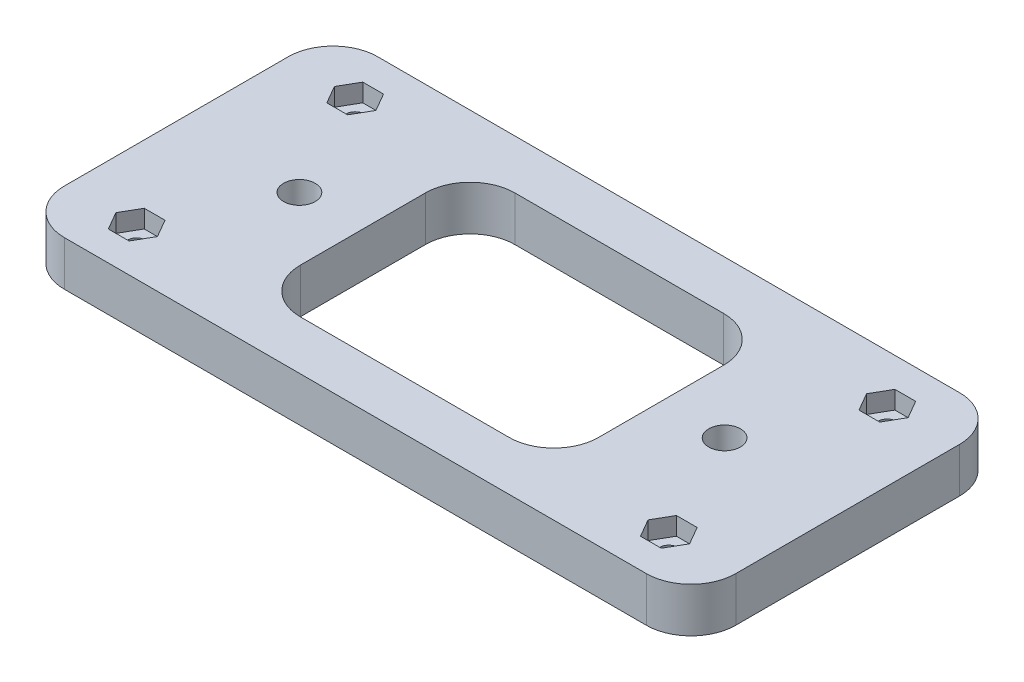
SolidWorks part; units mm, degrees
ref_plane "Front Plane" through (0, 0, 0) normal (0, 0, 1) x (1, 0, 0)
ref_plane "Top Plane" through (0, 0, 0) normal (0, 1, 0) x (1, 0, 0)
ref_plane "Right Plane" through (0, 0, 0) normal (1, 0, 0) x (0, 0, -1)
sketch "Sketch1" plane through (0, 0, 0) normal (0, 1, 0) x (1, 0, 0)
  line L0 (-47.625, 0) -> (47.625, 0) construction
  line L1 (41.275, 22.225) -> (-41.275, 22.225)
  line L2 (47.625, 15.875) -> (47.625, -15.875)
  line L3 (41.275, -22.225) -> (-41.275, -22.225)
  line L4 (-47.625, 15.875) -> (-47.625, -15.875)
  line L5 (47.625, 22.225) -> (-47.625, -22.225) construction
  line L6 (47.625, -22.225) -> (-47.625, 22.225) construction
  line L7 (0, 22.225) -> (0, -22.225) construction
  arc A0 (41.275, 22.225) -> (47.625, 15.875) centre (41.275, 15.875) cw
  arc A1 (47.625, -15.875) -> (41.275, -22.225) centre (41.275, -15.875) cw
  arc A2 (-41.275, -22.225) -> (-47.625, -15.875) centre (-41.275, -15.875) cw
  arc A3 (-41.275, 22.225) -> (-47.625, 15.875) centre (-41.275, 15.875) ccw
  circle A6 centre (-37.75, 15.5) radius 1.3
  circle A7 centre (37.75, 15.5) radius 1.3
  circle A8 centre (37.75, -15.5) radius 1.3
  circle A9 centre (-37.75, -15.5) radius 1.3
  point P0 (0, 0)
  point P34 (0, 0)
  point P35 (0, 0)
  point P36 (0, 0)
  point P37 (0, 0)
  point P38 (0, 0)
  dimension "D3" = 6.35
  dimension "D4" = 2.6
  dimension "D5" = 75.5
  dimension "D6" = 31
  dimension "D1" = 44.45
  dimension "D2" = 95.25
extrude "Boss-Extrude1" add sketch "Sketch1" along normal blind 6.35
sketch "Sketch2" plane through (0, 6.35, 0) normal (0, 1, 0) x (1, 0, 0)
  line L0 (-47.625, 0) -> (0, 0) construction
  line L1 (-34.8055, 15.5) -> (-36.2778, 18.05)
  line L2 (-36.2778, 18.05) -> (-39.2222, 18.05)
  line L3 (-39.2222, 18.05) -> (-40.6945, 15.5)
  line L4 (-40.6945, 15.5) -> (-39.2222, 12.95)
  line L5 (-39.2222, 12.95) -> (-36.2778, 12.95)
  line L6 (-36.2778, 12.95) -> (-34.8055, 15.5)
  line L7 (-47.625, 15.875) -> (-47.625, -15.875) construction
  line L8 (0, 0) -> (0, 22.225) construction
  line L9 (41.275, 22.225) -> (-41.275, 22.225) construction
  line L10 (36.2778, 12.95) -> (34.8055, 15.5)
  line L11 (39.2222, 12.95) -> (36.2778, 12.95)
  line L12 (40.6945, 15.5) -> (39.2222, 12.95)
  line L13 (39.2222, 18.05) -> (40.6945, 15.5)
  line L14 (36.2778, 18.05) -> (39.2222, 18.05)
  line L15 (34.8055, 15.5) -> (36.2778, 18.05)
  line L16 (34.8055, -15.5) -> (36.2778, -18.05)
  line L17 (36.2778, -18.05) -> (39.2222, -18.05)
  line L18 (39.2222, -18.05) -> (40.6945, -15.5)
  line L19 (40.6945, -15.5) -> (39.2222, -12.95)
  line L20 (39.2222, -12.95) -> (36.2778, -12.95)
  line L21 (36.2778, -12.95) -> (34.8055, -15.5)
  line L22 (-36.2778, -12.95) -> (-34.8055, -15.5)
  line L23 (-39.2222, -12.95) -> (-36.2778, -12.95)
  line L24 (-40.6945, -15.5) -> (-39.2222, -12.95)
  line L25 (-39.2222, -18.05) -> (-40.6945, -15.5)
  line L26 (-36.2778, -18.05) -> (-39.2222, -18.05)
  line L27 (-34.8055, -15.5) -> (-36.2778, -18.05)
  circle A0 centre (-37.75, 15.5) radius 2.55 construction
  circle A1 centre (37.75, 15.5) radius 2.55 construction
  circle A2 centre (37.75, -15.5) radius 2.55 construction
  circle A3 centre (-37.75, -15.5) radius 2.55 construction
  dimension "D1" = 5.1
extrude "Cut-Extrude1" cut sketch "Sketch2" against normal blind 2.55
hole_wizard "CSK for #8 Flat Head Machine Screw (100)4" positions "Sketch4" profile "Sketch5" countersink size "#8" standard "ANSI Inch" end condition through all
sketch "Sketch4" plane through (0, 0, 0) normal (0, -1, 0) x (-1, 0, 0)
  line L0 (30.1625, 0) -> (-30.1625, 0) construction
  point P0 (30.1625, 0)
  point P2 (-30.1625, 0)
  dimension "D1" = 60.325
sketch "Sketch5" plane through (-30.1625, 0, 0) normal (1, 0, 0) x (0, 0, -1)
  line L0 (0, 0) -> (0, 6.35)
  line L1 (0, 6.35) -> (2.2479, 6.35)
  line L2 (2.2479, 6.35) -> (2.2479, 1.6518)
  line L3 (2.2479, 1.6518) -> (4.2164, 0)
  line L5 (4.2164, 0) -> (0, 0)
  line L6 (-2.2479, 1.6518) -> (-4.2164, 0) construction
  line L11 (0, -6.35) -> (0, 107.95) construction
  dimension "Thru Hole Dia." = 4.4958
  dimension "Thru Hole Depth" = 6.35
  dimension "Near C'Sink Dia." = 8.4328
  dimension "Near C'Sink Angle" = 100
sketch "Sketch6" plane through (0, 0, 0) normal (0, -1, 0) x (1, 0, 0)
  line L0 (41.275, -22.225) -> (-41.275, -22.225) construction
  line L1 (-14.8125, -15.225) -> (14.8125, -15.225)
  line L2 (-21.1625, -8.875) -> (-21.1625, 8.875)
  line L3 (-14.8125, 15.225) -> (14.8125, 15.225)
  line L4 (21.1625, -8.875) -> (21.1625, 8.875)
  line L5 (-21.1625, -15.225) -> (21.1625, 15.225) construction
  line L6 (-21.1625, 15.225) -> (21.1625, -15.225) construction
  circle A0 centre (30.1625, 0) radius 4.2164 construction
  arc A1 (-21.1625, 8.875) -> (-14.8125, 15.225) centre (-14.8125, 8.875) cw
  arc A2 (-14.8125, -15.225) -> (-21.1625, -8.875) centre (-14.8125, -8.875) cw
  arc A3 (14.8125, -15.225) -> (21.1625, -8.875) centre (14.8125, -8.875) ccw
  arc A4 (14.8125, 15.225) -> (21.1625, 8.875) centre (14.8125, 8.875) cw
  point P0 (0, 0)
  dimension "D3" = 6.35
  dimension "D1" = 7
  dimension "D2" = 9
extrude "Cut-Extrude2" cut sketch "Sketch6" against normal through all both and the other way through all
